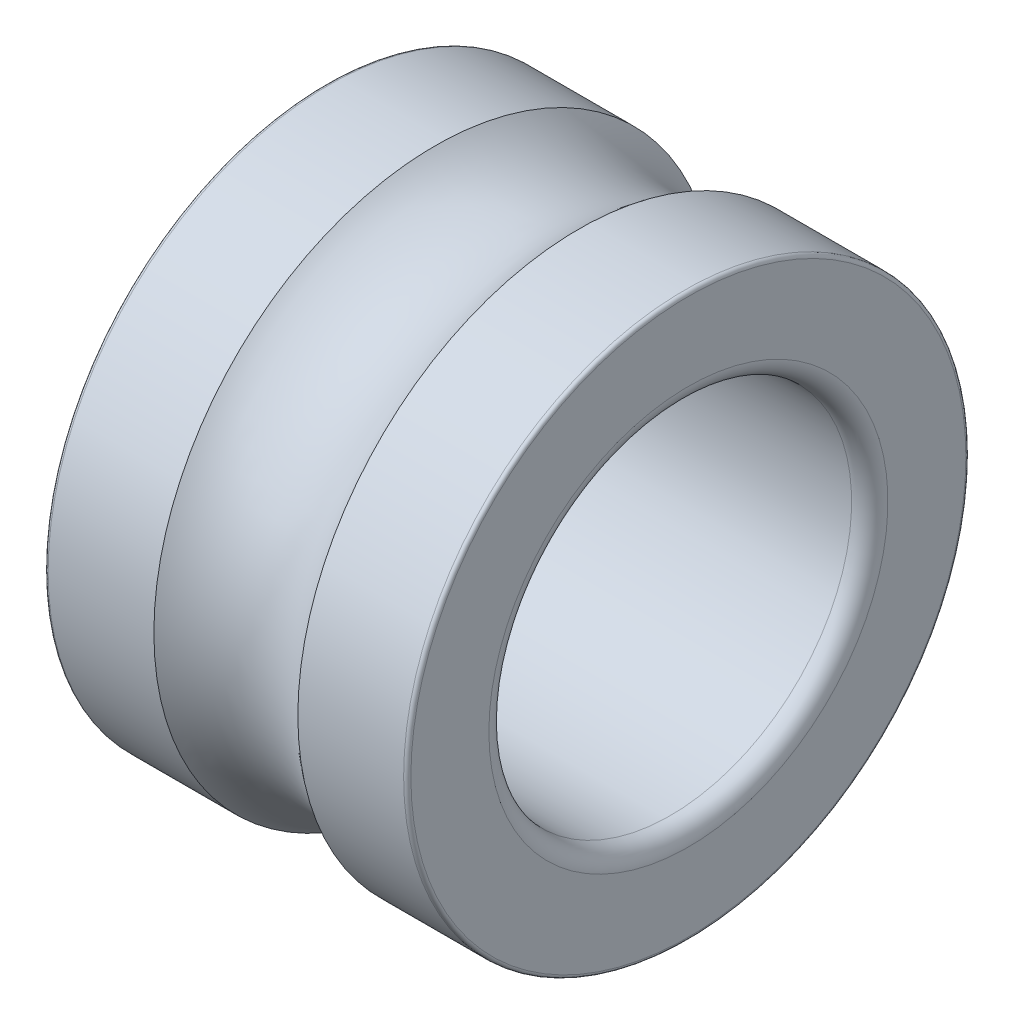
SolidWorks part; units mm, degrees
ref_plane "Front Plane" through (0, 0, 0) normal (0, 0, 1) x (1, 0, 0)
ref_plane "Top Plane" through (0, 0, 0) normal (0, 1, 0) x (1, 0, 0)
ref_plane "Right Plane" through (0, 0, 0) normal (1, 0, 0) x (0, 0, -1)
ref_plane "Plane1" through (0, 0, 0) normal (0, 0, 1) x (1, 0, 0)
sketch "Sketch1" plane through (0, 0, 0) normal (0, 0, 1) x (1, 0, 0)
  line L0 (0, 0.765) -> (0, 0.55)
  line L1 (0.05, 0.5) -> (0.95, 0.5)
  line L2 (1, 0.55) -> (1, 0.765)
  line L3 (0.99, 0.775) -> (0.6984, 0.775)
  line L4 (0.3016, 0.775) -> (0.01, 0.775)
  line L5 (50, 0) -> (-50, 0) construction
  arc A0 (0, 0.55) -> (0.05, 0.5) centre (0.05, 0.55) ccw
  arc A1 (0.95, 0.5) -> (1, 0.55) centre (0.95, 0.55) ccw
  arc A2 (1, 0.765) -> (0.99, 0.775) centre (0.99, 0.765) ccw
  arc A3 (0.6984, 0.775) -> (0.3016, 0.775) centre (0.5, 1) cw
  arc A4 (0.01, 0.775) -> (0, 0.765) centre (0.01, 0.765) ccw
revolve "Revolve1" add sketch "Sketch1" angle 360 about L5
